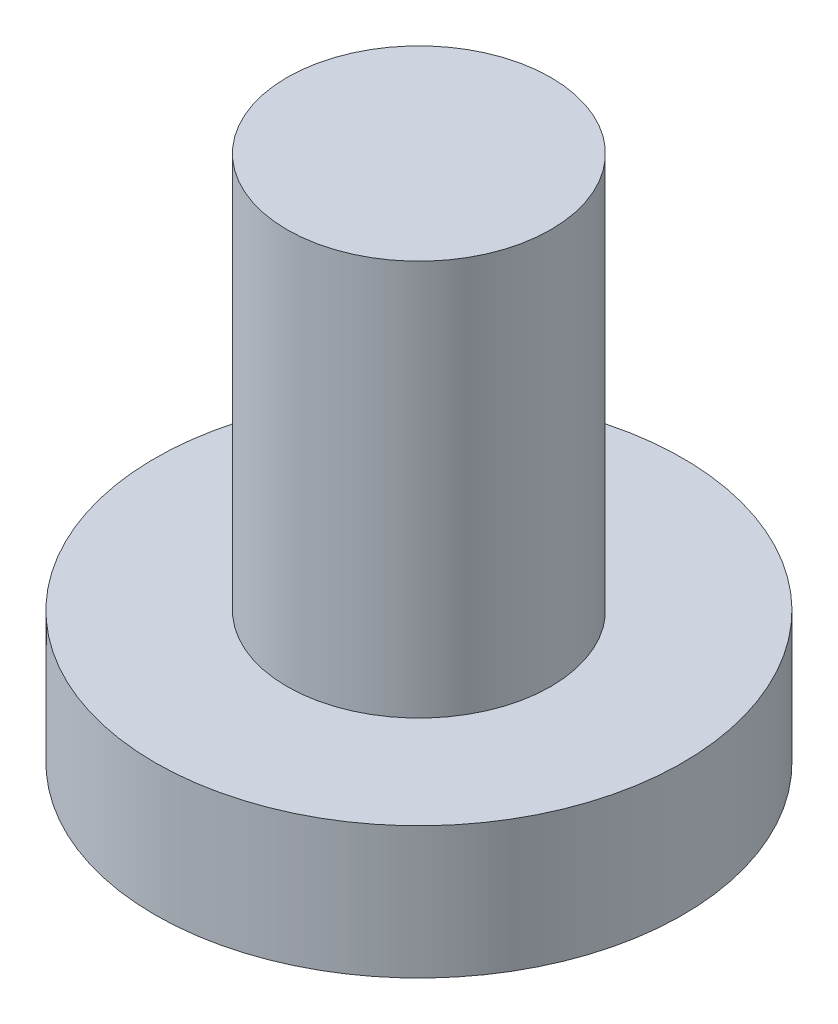
SolidWorks part; units mm, degrees
ref_plane "Front Plane" through (0, 0, 0) normal (0, 0, 1) x (1, 0, 0)
ref_plane "Top Plane" through (0, 0, 0) normal (0, 1, 0) x (1, 0, 0)
ref_plane "Right Plane" through (0, 0, 0) normal (1, 0, 0) x (0, 0, -1)
sketch "Sketch2" plane through (0, 0, 0) normal (0, 1, 0) x (1, 0, 0)
  circle A0 centre (0, 0) radius 2
  dimension "D1" = 4
extrude "Boss-Extrude1" add sketch "Sketch2" along normal blind 1
sketch "Sketch3" plane through (0, 1, 0) normal (0, 1, 0) x (1, 0, 0)
  circle A0 centre (0, 0) radius 1
  dimension "D1" = 2
extrude "Boss-Extrude3" add sketch "Sketch3" along normal blind 3 contours A0
